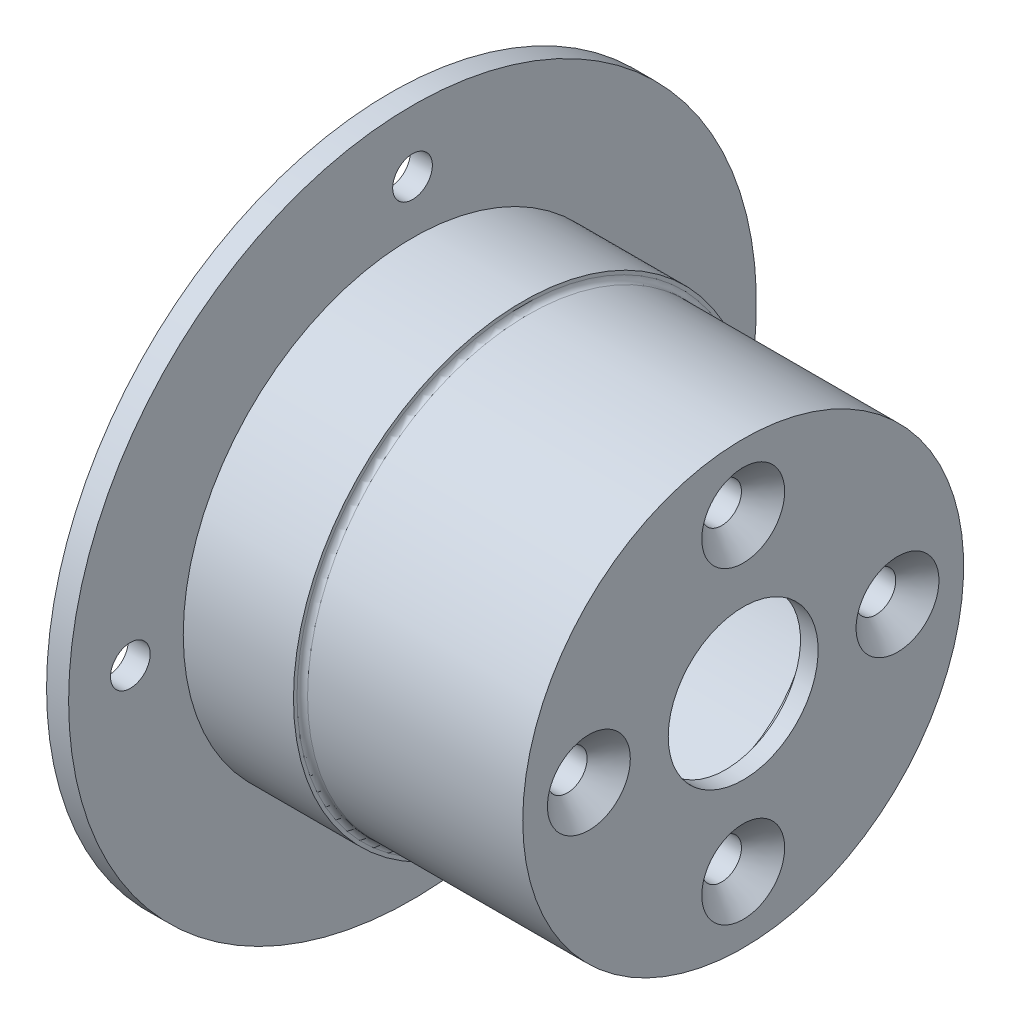
SolidWorks part; units mm, degrees
material "6061 Alloy"
ref_plane "Front Plane" through (0, 0, 0) normal (0, 0, 1) x (1, 0, 0)
ref_plane "Top Plane" through (0, 0, 0) normal (0, 1, 0) x (1, 0, 0)
ref_plane "Right Plane" through (0, 0, 0) normal (1, 0, 0) x (0, 0, -1)
sketch "Sketch2" plane through (0, 0, 0) normal (0, 0, 1) x (1, 0, 0)
  line L0 (-64.1034, 0) -> (113.4236, 0) construction
  line L2 (0, 21) -> (35, 21)
  line L3 (0, -55) -> (0, 55) construction
  line L13 (35, 21) -> (35, 12.5)
  line L14 (35, 12.5) -> (38, 12.5)
  line L19 (15, 25) -> (15, 26)
  line L21 (0, 26) -> (0, 21)
  line L25 (40, 25) -> (15, 25)
  line L26 (15, 26) -> (2.5, 26)
  line L27 (2.5, 26) -> (2.5, 39)
  line L28 (2.5, 39) -> (0, 39)
  line L29 (0, 39) -> (0, 26)
  line L30 (38, 12.5) -> (38, 8.5)
  line L31 (38, 8.5) -> (40, 8.5)
  line L32 (40, 8.5) -> (40, 25)
  point P14 (36.5, 12.5)
  dimension "D1" = 21
  dimension "D2" = 35
  dimension "D3" = 12.5
  dimension "D4" = 3
  dimension "D5" = 25
  dimension "D6" = 26
  dimension "D7" = 2.5
  dimension "D8" = 39
  dimension "D9" = 15
  dimension "D10" = 8.5
  dimension "D11" = 2
revolve "Revolve1" add sketch "Sketch2" angle 360 about L0
hole_wizard "CSK for M4 Flat Head Machine Screw1" positions "Sketch7" profile "Sketch8" countersink size "M4" standard "ANSI Metric" end condition up to next
sketch "Sketch7" plane through (40, 0, 0) normal (1, 0, 0) x (0, 0, -1)
  circle A0 centre (0, 0) radius 17.5
  point P0 (0, 17.5)
  point P2 (17.5, 0)
  point P4 (0, -17.5)
  point P6 (-17.5, 0)
  dimension "D1" = 35
sketch "Sketch8" plane through (40, 17.5, 0) normal (0, 1, 0) x (0, 0, -1)
  line L0 (0, 0) -> (0, 5)
  line L1 (0, 5) -> (2.25, 5)
  line L2 (2.25, 5) -> (2.25, 2.45)
  line L3 (2.25, 2.45) -> (4.7, 0)
  line L5 (4.7, 0) -> (0, 0)
  line L6 (-2.25, 2.45) -> (-4.7, 0) construction
  line L11 (0, -6.35) -> (0, 107.95) construction
  dimension "Thru Hole Dia." = 4.5
  dimension "Thru Hole Depth" = 5
  dimension "Near C'Sink Dia." = 9.4
  dimension "Near C'Sink Angle" = 90
fillet "Fillet1" radius 0.6 1 edges at (15, 0, 25)
hole_wizard "M4 Clearance Hole1" positions "Sketch5" profile "Sketch6" hole size "M4" standard "ANSI Metric" end condition up to next
sketch "Sketch5" plane through (0, 0, 0) normal (-1, 0, 0) x (0, 0, 1)
  circle A0 centre (0, 0) radius 32
  point P0 (0, 32)
  point P2 (0, -32)
  point P4 (32, 0)
  point P6 (-32, 0)
  dimension "D1" = 64
sketch "Sketch6" plane through (0, 32, 0) normal (0, 1, 0) x (0, 0, 1)
  line L0 (0, 0) -> (0, 2.5)
  line L1 (0, 2.5) -> (2.25, 2.5)
  line L2 (2.25, 2.5) -> (2.25, 0)
  line L5 (2.25, 0) -> (0, 0)
  line L11 (0, -6.35) -> (0, 107.95) construction
  dimension "Thru Hole Dia." = 4.5
  dimension "Thru Hole Depth" = 2.5
